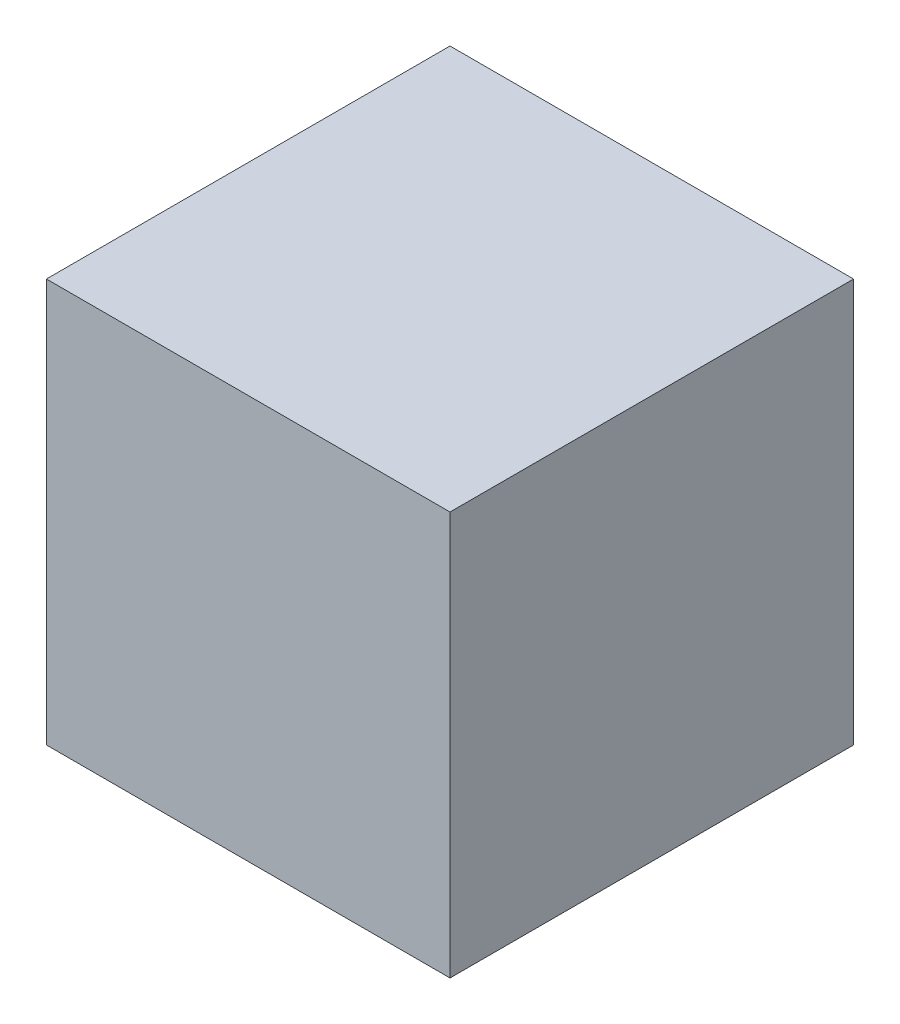
SolidWorks part; units mm, degrees
ref_plane "Front Plane" through (0, 0, 0) normal (0, 0, 1) x (1, 0, 0)
ref_plane "Top Plane" through (0, 0, 0) normal (0, 1, 0) x (1, 0, 0)
ref_plane "Right Plane" through (0, 0, 0) normal (1, 0, 0) x (0, 0, -1)
sketch "Sketch1" plane through (0, 0, 0) normal (0, 0, 1) x (1, 0, 0)
  line L0 (19.3434, 74.8609) -> (96.7169, 74.8609) construction
sketch "Sketch2" plane through (0, 0, 0) normal (0, 0, 1) x (1, 0, 0)
  line L0 (0, 0) -> (10, 0)
  line L1 (0, 0) -> (0, 10)
  line L2 (0, 10) -> (10, 10)
  line L3 (10, 0) -> (10, 10)
  dimension "D1" = 10
  dimension "D2" = 10
extrude "Boss-Extrude2" add sketch "Sketch2" along normal blind 10
